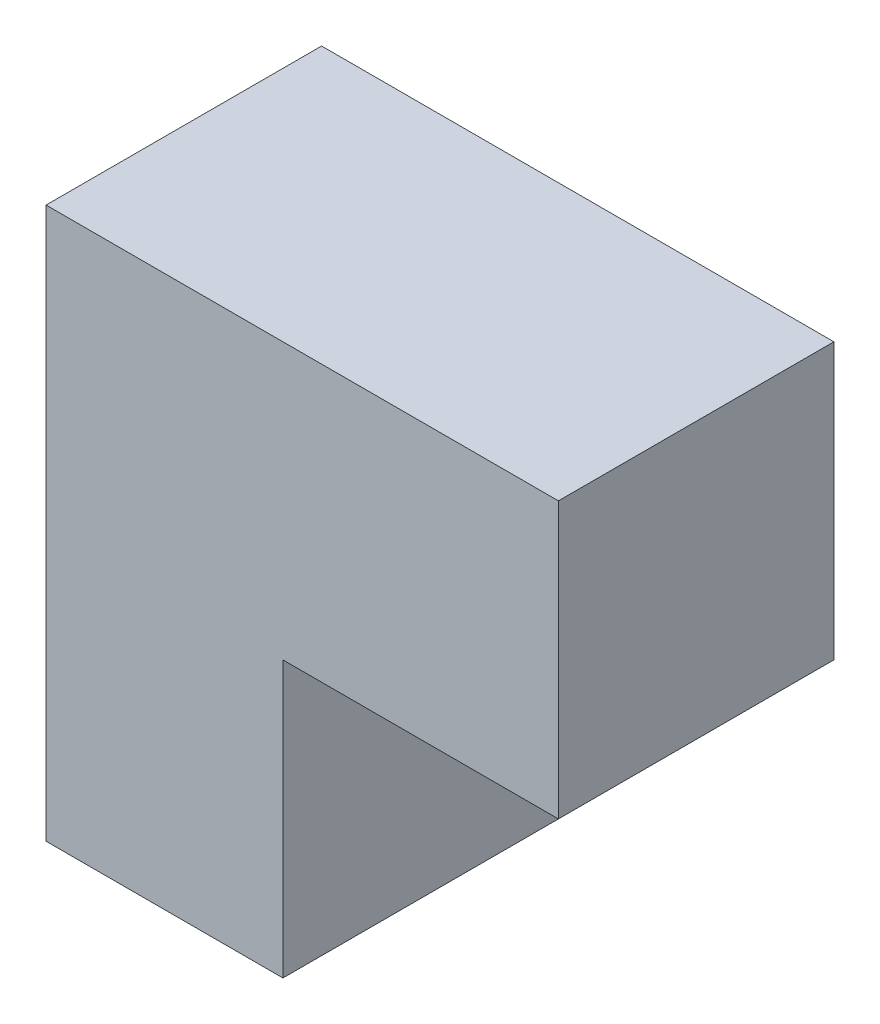
SolidWorks part; units mm, degrees
ref_plane "Plan de face" through (0, 0, 0) normal (0, 0, 1) x (1, 0, 0)
ref_plane "Plan de dessus" through (0, 0, 0) normal (0, 1, 0) x (1, 0, 0)
ref_plane "Plan de droite" through (0, 0, 0) normal (1, 0, 0) x (0, 0, -1)
sketch "Esquisse1" plane through (0, 0, 0) normal (0, 0, 1) x (1, 0, 0)
  line L0 (0, 0) -> (0, 60)
  line L1 (0, 60) -> (55.7906, 60)
  line L2 (55.7906, 60) -> (55.7906, 30)
  line L3 (55.7906, 30) -> (25.7906, 30)
  line L4 (25.7906, 30) -> (25.7906, 0)
  line L5 (25.7906, 0) -> (0, 0)
  dimension "D1" = 60
  dimension "D2" = 30
  dimension "D3" = 30
extrude "Boss.-Extru.1" add sketch "Esquisse1" along normal blind 30
